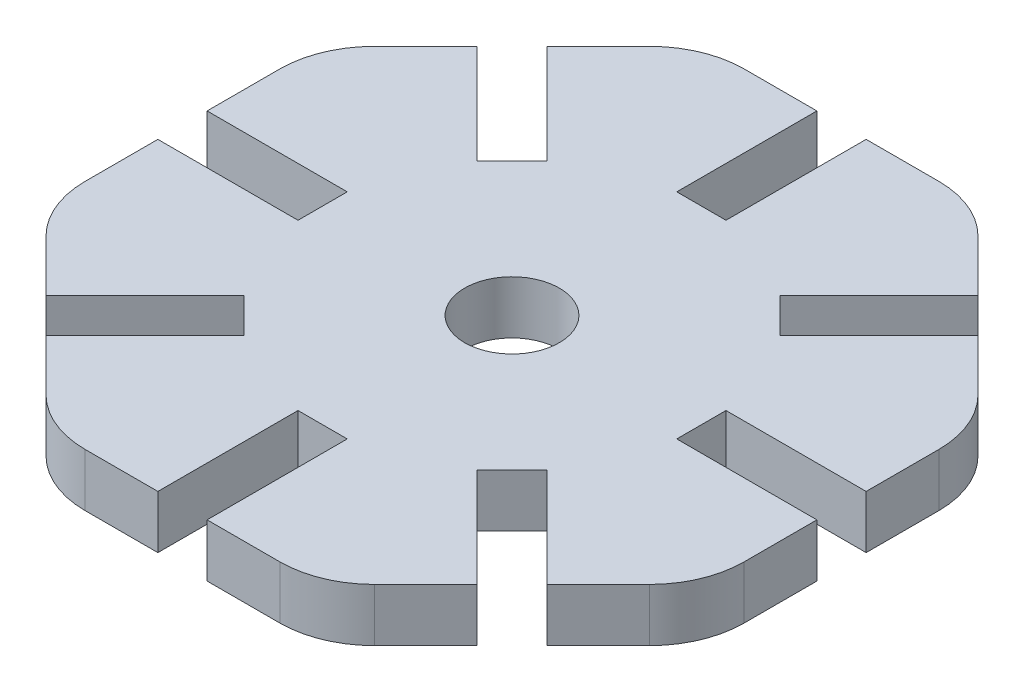
SolidWorks part; units mm, degrees
ref_plane "Ebene vorne" through (0, 0, 0) normal (0, 0, 1) x (1, 0, 0)
ref_plane "Ebene oben" through (0, 0, 0) normal (0, 1, 0) x (1, 0, 0)
ref_plane "Ebene rechts" through (0, 0, 0) normal (1, 0, 0) x (0, 0, -1)
sketch "Sketch1" plane through (0, 0, 0) normal (0, 1, 0) x (1, 0, 0)
  line L0 (-1.3, -17.4) -> (-1.3, -10)
  line L1 (17.4, -5.1362) -> (17.4, -1.3)
  line L2 (15.9355, 8.6718) -> (13.2229, 11.3844)
  line L3 (5.1362, 17.4) -> (1.3, 17.4)
  line L4 (-8.6718, 15.9355) -> (-11.3844, 13.2229)
  line L5 (-17.4, 5.1362) -> (-17.4, 1.3)
  line L6 (-15.9355, -8.6718) -> (-13.2229, -11.3844)
  line L7 (-5.1362, -17.4) -> (-1.3, -17.4)
  line L8 (8.6718, -15.9355) -> (11.3844, -13.2229)
  line L9 (-1.3, -10) -> (1.3, -10)
  line L10 (1.3, -10) -> (1.3, -17.4)
  line L11 (1.3, -17.4) -> (5.1362, -17.4)
  line L12 (-13.2229, -11.3844) -> (-7.9903, -6.1518)
  line L13 (-7.9903, -6.1518) -> (-6.1518, -7.9903)
  line L14 (-6.1518, -7.9903) -> (-11.3844, -13.2229)
  line L15 (-17.4, 1.3) -> (-10, 1.3)
  line L16 (-10, 1.3) -> (-10, -1.3)
  line L17 (-10, -1.3) -> (-17.4, -1.3)
  line L18 (-11.3844, 13.2229) -> (-6.1518, 7.9903)
  line L19 (-6.1518, 7.9903) -> (-7.9903, 6.1518)
  line L20 (-7.9903, 6.1518) -> (-13.2229, 11.3844)
  line L21 (1.3, 17.4) -> (1.3, 10)
  line L22 (1.3, 10) -> (-1.3, 10)
  line L23 (-1.3, 10) -> (-1.3, 17.4)
  line L24 (13.2229, 11.3844) -> (7.9903, 6.1518)
  line L25 (7.9903, 6.1518) -> (6.1518, 7.9903)
  line L26 (6.1518, 7.9903) -> (11.3844, 13.2229)
  line L27 (17.4, -1.3) -> (10, -1.3)
  line L28 (10, -1.3) -> (10, 1.3)
  line L29 (10, 1.3) -> (17.4, 1.3)
  line L30 (11.3844, -13.2229) -> (6.1518, -7.9903)
  line L31 (6.1518, -7.9903) -> (7.9903, -6.1518)
  line L32 (7.9903, -6.1518) -> (13.2229, -11.3844)
  line L33 (-13.2229, 11.3844) -> (-15.9355, 8.6718)
  line L34 (-1.3, 17.4) -> (-5.1362, 17.4)
  line L35 (11.3844, 13.2229) -> (8.6718, 15.9355)
  line L36 (17.4, 1.3) -> (17.4, 5.1362)
  line L37 (-17.4, -1.3) -> (-17.4, -5.1362)
  line L38 (-11.3844, -13.2229) -> (-8.6718, -15.9355)
  line L39 (13.2229, -11.3844) -> (15.9355, -8.6718)
  circle A0 centre (0, 0) radius 17.4 construction
  circle A1 centre (0, 0) radius 2.5
  arc A2 (5.1362, 17.4) -> (8.6718, 15.9355) centre (5.1362, 12.4) cw
  arc A3 (15.9355, 8.6718) -> (17.4, 5.1362) centre (12.4, 5.1362) cw
  arc A4 (17.4, -5.1362) -> (15.9355, -8.6718) centre (12.4, -5.1362) cw
  arc A5 (8.6718, -15.9355) -> (5.1362, -17.4) centre (5.1362, -12.4) cw
  arc A6 (-5.1362, -17.4) -> (-8.6718, -15.9355) centre (-5.1362, -12.4) cw
  arc A7 (-15.9355, -8.6718) -> (-17.4, -5.1362) centre (-12.4, -5.1362) cw
  arc A8 (-17.4, 5.1362) -> (-15.9355, 8.6718) centre (-12.4, 5.1362) cw
  arc A9 (-5.1362, 17.4) -> (-8.6718, 15.9355) centre (-5.1362, 12.4) ccw
  point P46 (0, 0)
extrude "Boss-Extrude1" add sketch "Sketch1" along normal blind 2.8
equation "\"D1@Sketch1\"=(\"D6@Sketch1\"+\"Slot Width\")/2"
equation "\"D2@Sketch1\"=(\"Slot Width\")/2"
equation "\"D6@Sketch1\"=20.0-(\"Slot Width\")"
